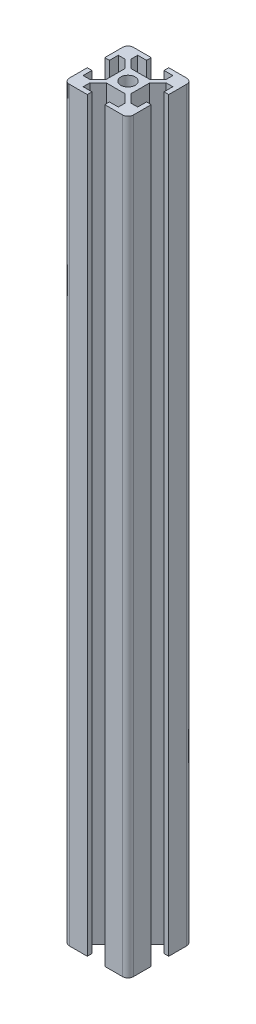
SolidWorks part; units mm, degrees
ref_plane "Front Plane" through (0, 0, 0) normal (0, 0, 1) x (1, 0, 0)
ref_plane "Top Plane" through (0, 0, 0) normal (0, 1, 0) x (1, 0, 0)
ref_plane "Right Plane" through (0, 0, 0) normal (1, 0, 0) x (0, 0, -1)
sketch "Sketch1" plane through (0, 0, 0) normal (0, 1, 0) x (1, 0, 0)
  line L0 (5.8, 4.3858) -> (5.8, -4.3858)
  line L1 (-12.5, 15) -> (-4.1, 15)
  line L2 (-15, 12.5) -> (-15, 4.1)
  line L3 (-12.5, -15) -> (-4.1, -15)
  line L4 (15, 12.5) -> (15, 4.1)
  line L5 (-15, 15) -> (15, -15) construction
  line L6 (-15, -15) -> (15, 15) construction
  line L7 (-5.8, 4.3858) -> (-5.8, -4.3858)
  line L8 (-4.3858, 5.8) -> (4.3858, 5.8)
  line L9 (-4.3858, -5.8) -> (4.3858, -5.8)
  line L10 (-8.25, -9.6642) -> (-4.3858, -5.8)
  line L11 (-9.6642, 8.25) -> (-5.8, 4.3858)
  line L12 (-9.6642, -8.25) -> (-5.8, -4.3858)
  line L13 (-8.25, 9.6642) -> (-4.3858, 5.8)
  line L14 (-8.25, 12.8) -> (-8.25, 9.6642)
  line L15 (-12.8, 8.25) -> (-9.6642, 8.25)
  line L16 (8.25, 12.8) -> (8.25, 9.6642)
  line L17 (9.6642, 8.25) -> (12.8, 8.25)
  line L18 (-12.8, -8.25) -> (-9.6642, -8.25)
  line L19 (-8.25, -9.6642) -> (-8.25, -12.8)
  line L20 (8.25, -9.6642) -> (8.25, -12.8)
  line L21 (9.6642, -8.25) -> (12.8, -8.25)
  line L22 (-14.2929, 15.7071) -> (15.7071, -14.2929) construction
  line L23 (-15.7071, 14.2929) -> (14.2929, -15.7071) construction
  line L24 (-12.8, 8.25) -> (-12.8, 4.1)
  line L25 (-15.7071, -14.2929) -> (14.2929, 15.7071) construction
  line L26 (12.8, 8.25) -> (12.8, 4.1)
  line L27 (-14.2929, -15.7071) -> (15.7071, 14.2929) construction
  line L28 (-8.25, -12.8) -> (-4.1, -12.8)
  line L29 (-8.25, 12.8) -> (-4.1, 12.8)
  line L30 (-15, -4.1) -> (-12.8, -4.1)
  line L31 (-15, 4.1) -> (-12.8, 4.1)
  line L32 (-4.1, 12.8) -> (-4.1, 15)
  line L33 (4.1, 15) -> (4.1, 12.8)
  line L34 (15, -4.1) -> (12.8, -4.1)
  line L35 (12.8, 4.1) -> (15, 4.1)
  line L36 (-4.1, -12.8) -> (-4.1, -15)
  line L37 (4.1, -12.8) -> (4.1, -15)
  line L38 (12.8, -4.1) -> (12.8, -8.25)
  line L39 (4.1, -12.8) -> (8.25, -12.8)
  line L40 (-12.8, -4.1) -> (-12.8, -8.25)
  line L41 (4.1, 12.8) -> (8.25, 12.8)
  line L42 (5.8, 4.3858) -> (9.6642, 8.25)
  line L43 (4.3858, 5.8) -> (8.25, 9.6642)
  line L48 (4.3858, -5.8) -> (8.25, -9.6642)
  line L49 (5.8, -4.3858) -> (9.6642, -8.25)
  line L50 (15, -4.1) -> (15, -12.5)
  line L51 (4.1, -15) -> (12.5, -15)
  line L52 (-15, -4.1) -> (-15, -12.5)
  line L53 (4.1, 15) -> (12.5, 15)
  circle A0 centre (0, 0) radius 3.4
  arc A1 (-12.5, 15) -> (-15, 12.5) centre (-12.5, 12.5) ccw
  arc A2 (-15, -12.5) -> (-12.5, -15) centre (-12.5, -12.5) ccw
  arc A3 (12.5, -15) -> (15, -12.5) centre (12.5, -12.5) ccw
  arc A4 (12.5, 15) -> (15, 12.5) centre (12.5, 12.5) cw
  point P0 (0, 0)
  point P22 (5.8, 0)
  point P24 (0, 5.8)
  point P26 (-5.8, 0)
  point P29 (0, -5.8)
  dimension "D30" = 6.8
  dimension "D31" = 2.5
  dimension "D1" = 30
  dimension "D2" = 30
  dimension "D3" = 9.2
  dimension "D4" = 9.2
  dimension "D5" = 9.2
  dimension "D6" = 9.2
  dimension "D7" = 1
  dimension "D9" = 16.5
  dimension "D10" = 4.1
  dimension "D11" = 16.5
  dimension "D12" = 4.1
  dimension "D13" = 16.5
  dimension "D14" = 8.25
  dimension "D15" = 16.5
  dimension "D16" = 4.1
  dimension "D17" = 2.2
  dimension "D18" = 2.2
  dimension "D19" = 2.2
  dimension "D20" = 2.2
  dimension "D21" = 8.2
  dimension "D22" = 8.25
  dimension "D23" = 8.2
  dimension "D24" = 8.25
  dimension "D25" = 8.2
  dimension "D26" = 8.25
  dimension "D27" = 8.2
  dimension "D28" = 4.1
  dimension "D29" = 2
  dimension "D8" = 1
extrude "Boss-Extrude1" add sketch "Sketch1" along normal blind 350
